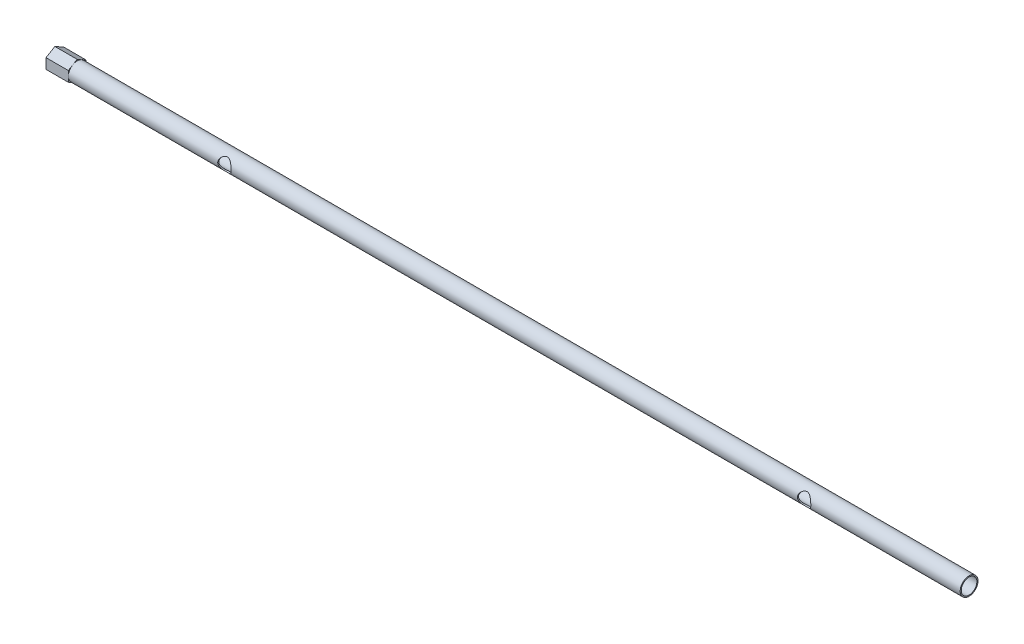
SolidWorks part; units mm, degrees
ref_plane "Front Plane" through (0, 0, 0) normal (0, 0, 1) x (1, 0, 0)
ref_plane "Top Plane" through (0, 0, 0) normal (0, 1, 0) x (1, 0, 0)
ref_plane "Right Plane" through (0, 0, 0) normal (1, 0, 0) x (0, 0, -1)
sketch "Sketch2" plane through (0, 0, 0) normal (0, 1, 0) x (1, 0, 0)
  line L0 (-100, 0) -> (100, 0)
  point P3 (0, 0)
  dimension "D1" = 200
sweep "Sweep1" add path "Sketch2" circular profile diameter 4 parameters "D3"=4
sketch "Sketch9" plane through (-100, 0, 0) normal (-1, 0, 0) x (0, 0, 1)
  line L1 (1.9883, -1.1748) -> (2.0115, 1.1345)
  line L2 (2.0115, 1.1345) -> (0.0233, 2.3093)
  line L3 (0.0233, 2.3093) -> (-1.9883, 1.1748)
  line L4 (-1.9883, 1.1748) -> (-2.0115, -1.1345)
  line L5 (-2.0115, -1.1345) -> (-0.0233, -2.3093)
  line L6 (-0.0233, -2.3093) -> (1.9883, -1.1748)
  circle A0 centre (0, 0) radius 2 construction
  circle A1 centre (0, 0) radius 2 construction
  dimension "D1" = 4
  dimension "D2" = 0.0233
extrude "Boss-Extrude1" add sketch "Sketch9" along normal blind 5
sketch "Sketch10" plane through (100, 0, 0) normal (1, 0, 0) x (0, 0, -1)
  circle A0 centre (0, 0) radius 1.75
  dimension "D1" = 3.5
extrude "Cut-Extrude1" cut sketch "Sketch10" against normal blind 200
ref_plane "Plane1" through (0, 0, 2) normal (0, 0, 1) x (1, 0, 0)
sketch "Sketch35" plane through (0, 0, 2) normal (0, 0, 1) x (1, 0, 0)
  line L0 (100, -2) -> (100, 2) construction
  line L1 (0, 33.2525) -> (0, -21.8774) construction
  circle A0 centre (65, 0) radius 1.5
  circle A1 centre (-65, 0) radius 1.5
  dimension "D1" = 3
  dimension "D2" = 35
extrude "Cut-Extrude3" cut sketch "Sketch35" against normal up to surface (0.25 mm away)
